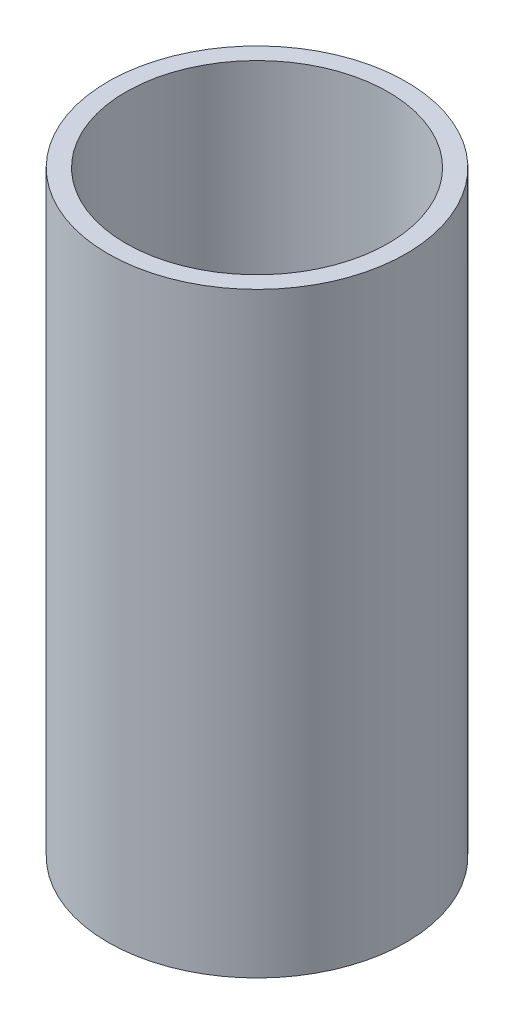
SolidWorks part; units mm, degrees
ref_plane "Front Plane" through (0, 0, 0) normal (0, 0, 1) x (1, 0, 0)
ref_plane "Top Plane" through (0, 0, 0) normal (0, 1, 0) x (1, 0, 0)
ref_plane "Right Plane" through (0, 0, 0) normal (1, 0, 0) x (0, 0, -1)
sketch "Sketch1" plane through (0, 0, 0) normal (0, 1, 0) x (1, 0, 0)
  circle A0 centre (0, 0) radius 12.7
  circle A1 centre (0, 0) radius 11.176
  dimension "D1" = 25.4
  dimension "D2" = 22.352
extrude "Boss-Extrude1" add sketch "Sketch1" along normal blind 50.8
